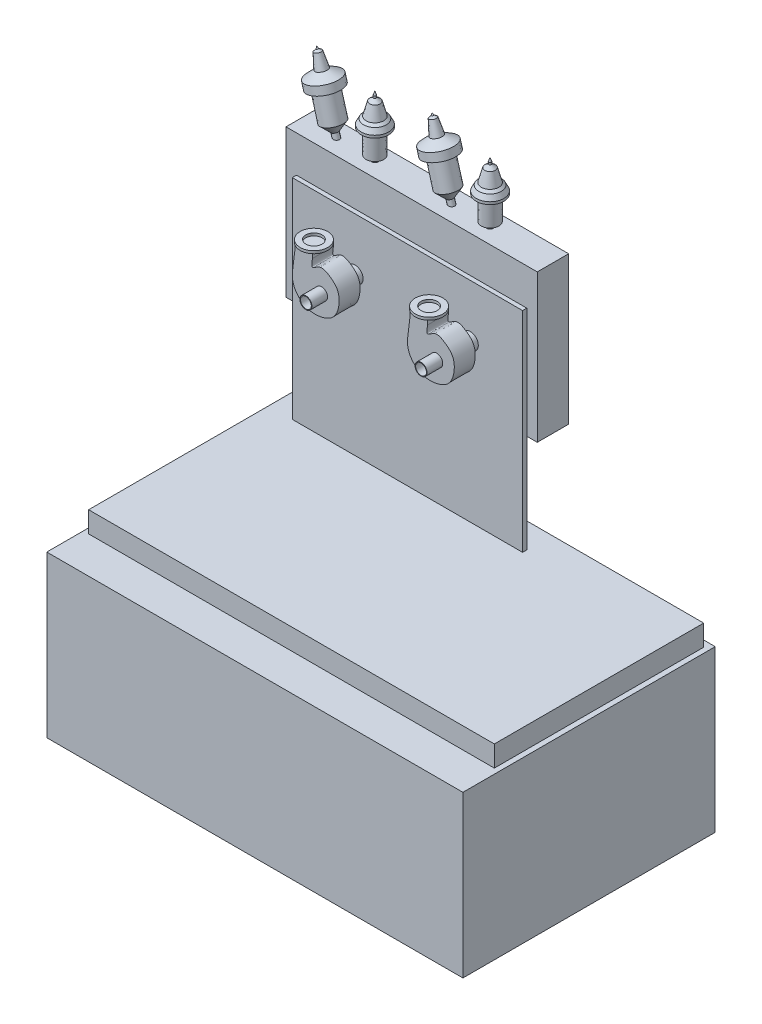
SolidWorks part; units mm, degrees
ref_plane "Front Plane" through (0, 0, 0) normal (0, 0, 1) x (1, 0, 0)
ref_plane "Top Plane" through (0, 0, 0) normal (0, 1, 0) x (1, 0, 0)
ref_plane "Right Plane" through (0, 0, 0) normal (1, 0, 0) x (0, 0, -1)
sketch "Sketch1" plane through (0, 0, 0) normal (0, 0, 1) x (1, 0, 0)
  line L0 (3050, 0) -> (-925, 0) construction
  line L2 (3050, 0) -> (-925, 0)
  line L3 (3050, 0) -> (3050, 100)
  line L4 (3050, 100) -> (-925, 100)
  line L5 (-925, 0) -> (-925, 100)
  dimension "D1" = 100
  dimension "D2" = 3975
  dimension "D3" = 3050
extrude "Extrude1" add sketch "Sketch1" along normal blind 2410
sketch "Sketch2" plane through (0, 100, 0) normal (0, 1, 0) x (1, 0, 0)
  line L0 (3050, 0) -> (-925, 0) construction
  line L1 (-875, -60) -> (3000, -60)
  line L2 (-875, -60) -> (-875, -2060)
  line L3 (-875, -2060) -> (3000, -2060)
  line L4 (3000, -60) -> (3000, -2060)
  line L5 (-925, -2410) -> (-925, 0) construction
  line L6 (3050, -2410) -> (3050, 0) construction
  dimension "D1" = 60
  dimension "D2" = 50
  dimension "D3" = 50
  dimension "D4" = 2000
extrude "Extrude2" add sketch "Sketch2" along normal blind 200
sketch "Sketch3" plane through (0, 0, 0) normal (0, 0, -1) x (-1, 0, 0)
  line L0 (-3000, 300) -> (-3000, 100) construction
  line L1 (-1650, 2650) -> (750, 2650)
  line L2 (-1650, 2650) -> (-1650, 1240)
  line L3 (-1650, 1240) -> (750, 1240)
  line L4 (750, 2650) -> (750, 1240)
  line L5 (851.3708, 1800) -> (-3127.4899, 1800) construction
  line L7 (-3000, 300) -> (875, 300) construction
  dimension "D1" = 1410
  dimension "D2" = 2400
  dimension "D3" = 1350
  dimension "D4" = 1500
  dimension "D5" = 850
extrude "Extrude3" add sketch "Sketch3" against normal blind 300
shell "Shell1" thickness 10
sketch "Sketch4" plane through (0, 0, 300) normal (0, 0, 1) x (1, 0, 0)
  line L0 (-875, 300) -> (3000, 300) construction
  line L1 (-650, 2300) -> (1550, 2300)
  line L2 (-650, 2300) -> (-650, 300)
  line L3 (-650, 300) -> (1550, 300)
  line L4 (1550, 2300) -> (1550, 300)
  line L5 (1650, 2650) -> (1650, 1240) construction
  line L6 (-750, 1240) -> (-750, 2650) construction
  line L7 (-750, 2650) -> (1650, 2650) construction
  dimension "D1" = 100
  dimension "D2" = 100
  dimension "D3" = 350
extrude "Extrude4" add sketch "Sketch4" along normal blind 40
sketch "Sketch5" plane through (0, 0, 290) normal (0, 0, -1) x (-1, 0, 0)
  line L0 (993.5382, 1800) -> (-2542.1999, 1800) construction
  line L1 (750, 2650) -> (-1650, 2650) construction
  line L2 (-1650, 2650) -> (-1650, 1240) construction
  arc A0 (-43.3819, 2031.9048) -> (143.3819, 2031.9048) centre (50, 1800) ccw
  arc A1 (143.3819, 2031.9048) -> (-43.3819, 2031.9048) centre (50, 2115) ccw
  dimension "D2" = 500
  dimension "D5" = 250
  dimension "D1" = 850
  dimension "D3" = 1700
  dimension "D4" = 315
extrude "Extrude5" add sketch "Sketch5" along normal blind 30
sketch "Sketch6" plane through (0, 0, 260) normal (0, 0, -1) x (-1, 0, 0)
  line L2 (50, 2115) -> (50, 1033.0864) construction
  circle A0 centre (50, 2115) radius 90.3356
  circle A1 centre (50, 1836.5812) radius 185.9941
  dimension "D1" = 278.4188
extrude "Extrude6" add sketch "Sketch6" along normal blind 250
sketch "Sketch7" plane through (0, 0, 10) normal (0, 0, -1) x (-1, 0, 0)
  line L0 (42.5, 2024.9762) -> (42.5, 1949.2246)
  line L1 (72.5, 2027.5113) -> (72.5, 1947.7091)
  line L2 (50, 2115) -> (50, 1800) construction
  arc A0 (72.5, 2027.5113) -> (42.5, 2024.9762) centre (50, 2115) ccw
  arc A1 (42.5, 1949.2246) -> (72.5, 1947.7091) centre (50, 1800) ccw
  dimension "D1" = 149.413
  dimension "D2" = 90.3356
  dimension "D3" = 30
  dimension "D4" = 15
extrude "Extrude7" add sketch "Sketch7" along normal blind 50
sketch "Sketch8" plane through (0, 0, -40) normal (0, 0, -1) x (-1, 0, 0)
  circle A0 centre (50, 1800) radius 84
  circle A1 centre (50, 1800) radius 77
  circle A2 centre (50, 2115) radius 57.15
  circle A3 centre (50, 2115) radius 48.6
  dimension "D1" = 168
  dimension "D2" = 154
  dimension "D3" = 114.3
  dimension "D4" = 97.2
extrude "Extrude8" add sketch "Sketch8" along normal blind 127
ref_plane "Plane1" through (0, 0, 150) normal (0, 0, 1) x (1, 0, 0)
sketch "Sketch9" plane through (0, 0, 150) normal (0, 0, 1) x (1, 0, 0)
  line L0 (-50, 2115) -> (-50, 3102.9) construction
  line L1 (-50, 2115) -> (-19.7824, 2115)
  line L2 (-19.7824, 2115) -> (-19.7824, 2668.294)
  line L3 (-19.7824, 2668.294) -> (32.6431, 2695.337)
  line L4 (32.6431, 2695.337) -> (32.6431, 2923.6257)
  line L5 (32.6431, 2923.6257) -> (80.9349, 2923.6257)
  line L6 (80.9349, 2923.6257) -> (80.9349, 2947.7716)
  line L7 (80.9349, 2947.7716) -> (56.789, 2994.5808)
  line L8 (56.789, 2994.5808) -> (32.6431, 3015.8192)
  line L9 (32.6431, 3015.8192) -> (-1.4, 3138.7438)
  line L10 (-1.4, 3138.7438) -> (-38.6259, 3167.4886)
  line L11 (-38.6259, 3167.4886) -> (-38.416, 3186.9112)
  line L12 (-38.416, 3186.9112) -> (-50.7701, 3222.157)
  line L13 (-50.7701, 3222.157) -> (-50, 2115)
  circle A0 centre (-50, 2115) radius 48.6 construction
revolve "Revolve2" add sketch "Sketch9" angle 360 about L13
sketch "Sketch10" plane through (0, 0, 150) normal (0, 0, 1) x (1, 0, 0)
  line L0 (-142.5477, 1682.7006) -> (-617.074, 3355.9179) construction
  line L1 (-104.2086, 1648.8632) -> (-403.442, 2703.9837)
  line L2 (-403.442, 2703.9837) -> (-352.9783, 2798.3695)
  line L3 (-352.9783, 2798.3695) -> (-420.1961, 3035.3848)
  line L4 (-420.1961, 3035.3848) -> (-378.3032, 3063.5034)
  line L5 (-378.3032, 3063.5034) -> (-399.2759, 3137.4546)
  line L6 (-399.2759, 3137.4546) -> (-506.9989, 3164.7536)
  line L7 (-506.9989, 3164.7536) -> (-563.1811, 3288.3677)
  line L8 (-563.1811, 3288.3677) -> (-591.006, 3298.3181)
  line L9 (-591.006, 3298.3181) -> (-605.6822, 3315.7496)
  line L10 (-605.6822, 3315.7496) -> (-135.461, 1640)
  line L11 (-135.461, 1640) -> (-104.2086, 1648.8632)
  line L12 (-104.2086, 1648.8632) -> (-105.9946, 1647.6506)
  line L13 (1640, 1250) -> (-740, 1250) construction
  arc A0 (-72.5, 1947.7091) -> (-42.5, 1949.2246) centre (-50, 1800) ccw construction
  dimension "D1" = 390
  dimension "D2" = 32.4849
  dimension "D3" = 1055.1205
  dimension "D4" = 1675.7496
revolve "Revolve3" add sketch "Sketch10" angle 360 about L10
pattern_linear "LPattern1" count 2 spacing 1100 along (1, 0, 0) of "Extrude5", "Extrude6", "Extrude7", "Extrude8", "Revolve2", "Revolve3"
sketch "Sketch11" plane through (0, 0, -40) normal (0, 0, -1) x (-1, 0, 0)
  circle A0 centre (-1050, 1800) radius 77 construction
  circle A1 centre (50, 1800) radius 77 construction
  circle A2 centre (-1050, 1800) radius 77
  circle A3 centre (50, 1800) radius 77
extrude "Extrude9" add sketch "Sketch11" against normal blind 530
sketch "Sketch12" plane through (0, 0, 340) normal (0, 0, 1) x (1, 0, 0)
  line L3 (-136.9075, 2086.6526) -> (-136.9075, 2048.1052)
  line L6 (-303.1431, 2086.6526) -> (-303.1431, 2048.1052)
  line L7 (-136.9075, 2086.6526) -> (-303.1431, 2086.6526)
  spline S0 degree 3 poles (-303.1431, 2048.1052) (-309.5686, 1998.6647) (-322.0586, 1902.5627) (-341.7384, 1744.7482) (-226.8576, 1599.2476) (-58.4172, 1590.9124) (76.6403, 1655.3577) (122.9056, 1780.292) (118.2583, 1910.2104) (29.2514, 1986.0843) (-61.9342, 2036.0157) (-153.6984, 1943.0384) (-142.6493, 2012.1762) (-136.9075, 2048.1052) knots 0 0 0 0 0.110148 0.214104 0.337659 0.464242 0.556489 0.644869 0.742352 0.817106 0.894893 0.945379 1 1 1 1
extrude "Extrude10" add sketch "Sketch12" along direction (0, 0, -1) on the side of the normal blind 200 from offset 120
sketch "Sketch13" plane through (0, 0, 660) normal (0, 0, 1) x (1, 0, 0)
  circle A0 centre (-50, 1800) radius 57.4
  circle A1 centre (-50, 1800) radius 84 construction
  circle A2 centre (-50, 1800) radius 51.8
  dimension "D1" = 114.8
  dimension "D2" = 5.6
extrude "Extrude11" add sketch "Sketch13" along normal blind 150
sketch "Sketch14" plane through (0, 2086.6526, 0) normal (0, 1, 0) x (1, 0, 0)
  circle A0 centre (-222.9868, -560.1152) radius 131.8584
  circle A1 centre (-222.9868, -560.1152) radius 77
  dimension "D1" = 154
extrude "Extrude12" add sketch "Sketch14" along normal blind 25
pattern_linear "LPattern2" count 2 spacing 1100 along (1, 0, 0) of "Extrude12", "Extrude10", "Extrude11"
sketch "Sketch15" plane through (0, 0, 0) normal (0, -1, 0) x (1, 0, 0)
  line L4 (-925, 0) -> (3050, 0)
  line L5 (3050, 0) -> (3050, 2410)
  line L6 (3050, 2410) -> (-925, 2410)
  line L7 (-925, 2410) -> (-925, 0)
  line L8 (-925, 0) -> (3050, 0)
  line L9 (3050, 0) -> (3050, 2410)
  line L10 (3050, 2410) -> (-925, 2410)
  line L11 (-925, 2410) -> (-925, 0)
  dimension "D1" = 0
extrude "Extrude13" add sketch "Sketch15" along normal blind 1436.15
